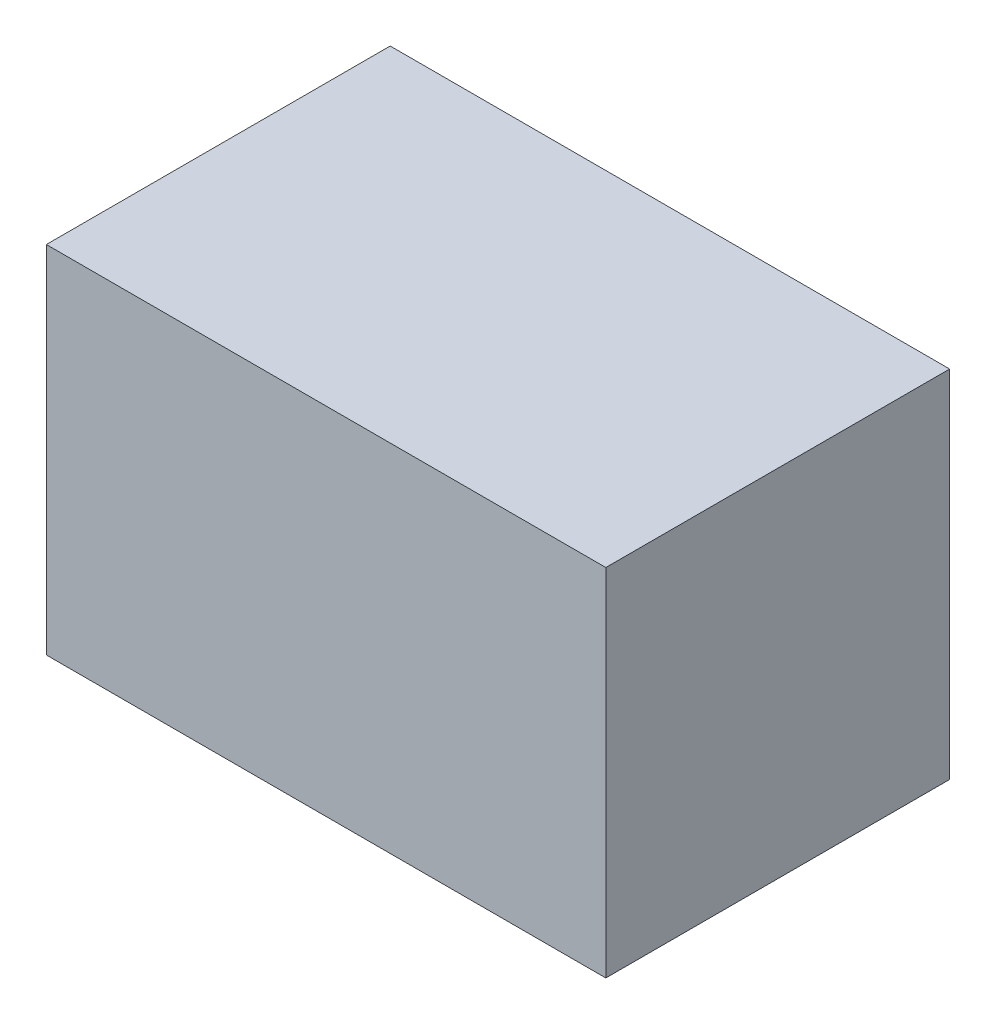
SolidWorks part; units mm, degrees
ref_plane "Front Plane" through (0, 0, 0) normal (0, 0, 1) x (1, 0, 0)
ref_plane "Top Plane" through (0, 0, 0) normal (0, 1, 0) x (1, 0, 0)
ref_plane "Right Plane" through (0, 0, 0) normal (1, 0, 0) x (0, 0, -1)
sketch "Sketch1" plane through (0, 0, 0) normal (0, 1, 0) x (1, 0, 0)
  line L1 (0, 0) -> (304.8, 0)
  line L2 (0, 0) -> (0, 187.325)
  line L3 (0, 187.325) -> (304.8, 187.325)
  line L4 (304.8, 0) -> (304.8, 187.325)
  dimension "D1" = 304.8
  dimension "D2" = 187.325
extrude "Boss-Extrude1" add sketch "Sketch1" along normal blind 193.675
